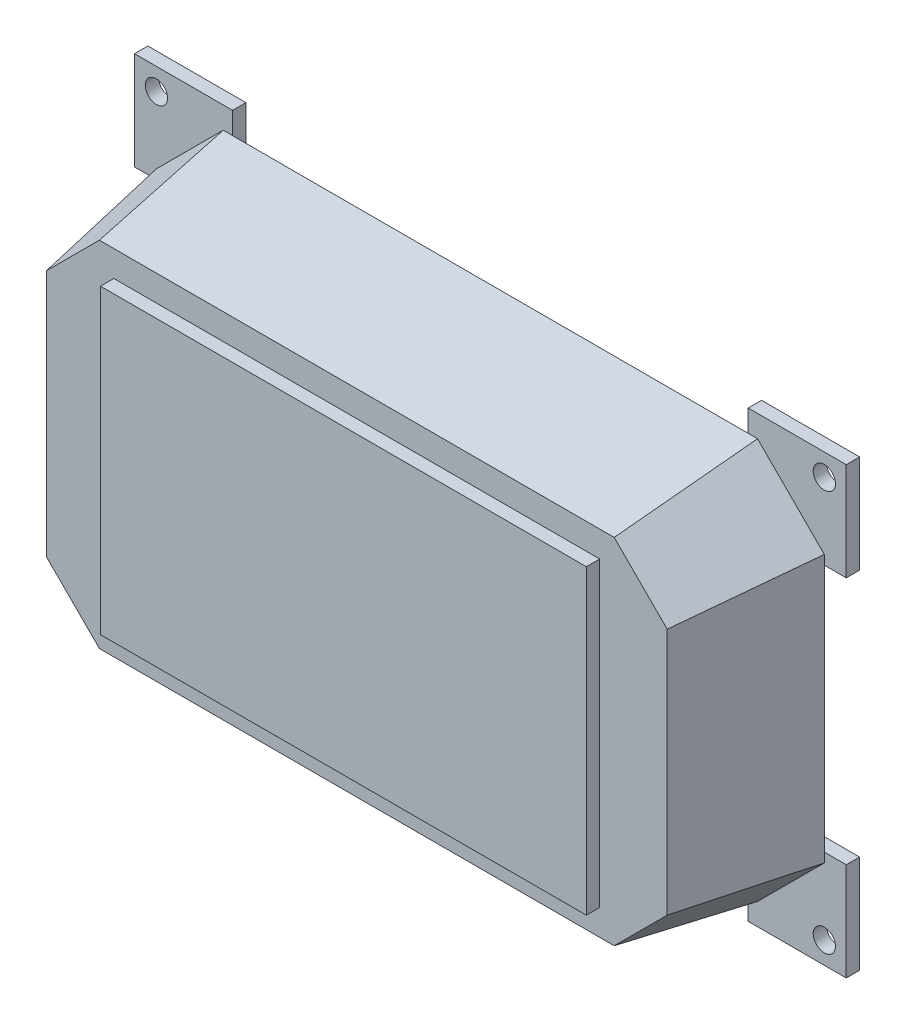
SolidWorks part; units mm, degrees
ref_plane "Front Plane" through (0, 0, 0) normal (0, 0, 1) x (1, 0, 0)
ref_plane "Top Plane" through (0, 0, 0) normal (0, 1, 0) x (1, 0, 0)
ref_plane "Right Plane" through (0, 0, 0) normal (1, 0, 0) x (0, 0, -1)
sketch "Sketch1" plane through (0, 0, 0) normal (0, 0, 1) x (1, 0, 0)
  line L0 (-100, 10.5319) -> (-85, 25.5319)
  line L1 (-85, 25.5319) -> (35, 25.5319)
  line L2 (-100, 10.5319) -> (-100, -49.4681)
  line L3 (-85, -64.4681) -> (35, -64.4681)
  line L4 (50, 10.5319) -> (50, -49.4681)
  line L5 (35, 25.5319) -> (50, 10.5319)
  line L6 (-100, -49.4681) -> (-85, -64.4681)
  line L7 (35, -64.4681) -> (50, -49.4681)
  point P0 (0, 0)
  point P1 (50, -64.4681)
  point P2 (-100, 25.5319)
  point P3 (-100, -64.4681)
  point P4 (50, 25.5319)
  dimension "D1" = 150
  dimension "D2" = 90
extrude "Boss-Extrude1" add sketch "Sketch1" along normal blind 30 draft 10
shell "Shell1" thickness 5
sketch "Sketch4" plane through (0, 0, -7) normal (0, 0, -1) x (-1, 0, 0)
  circle A0 centre (-24.7585, -65.1412) radius 1.5
  dimension "D1" = 3
extrude "Cut-Extrude1" cut sketch "Sketch4" against normal blind 15
ref_plane "Plane1" through (-26.0296, 0, 0) normal (1, 0, 0) x (0, 0, -1)
ref_plane "Plane2" through (0, -17.8507, 0) normal (0, 1, 0) x (1, 0, 0)
mirror "Mirror1" about plane through (-26.0296, 0, 0) normal (1, 0, 0) of "Cut-Extrude1"
sketch "Sketch5" plane through (0, 0, 30) normal (0, 0, 1) x (1, 0, 0)
  line L0 (32.8089, 20.2421) -> (-82.8089, 20.2421) construction
  line L1 (-79.5575, 14.4198) -> (29.5575, 14.4198)
  line L2 (-79.5575, 14.4198) -> (-79.5575, -53.356)
  line L3 (-79.5575, -53.356) -> (29.5575, -53.356)
  line L4 (29.5575, 14.4198) -> (29.5575, -53.356)
  line L5 (-79.5575, 14.4198) -> (29.5575, -53.356) construction
  line L6 (-79.5575, -53.356) -> (29.5575, 14.4198) construction
  line L7 (44.7102, -47.277) -> (44.7102, 8.3408) construction
  point P0 (-25, -19.4681)
  point P8 (-25, 20.2421)
  point P11 (44.7102, -19.4681)
  point P12 (29.5575, -19.4681)
extrude "Boss-Extrude3" add sketch "Sketch5" along normal blind 3
ref_plane "Plane3" through (0, -19.4681, 0) normal (0, 1, 0) x (1, 0, 0)
ref_plane "Plane4" through (-25, 0, 0) normal (1, 0, 0) x (0, 0, -1)
ref_plane "Plane5" through (0, -19.4681, 0) normal (0, 1, 0) x (1, 0, 0)
ref_plane "Plane6" through (-25, 0, 0) normal (-1, 0, 0) x (0, 0, 1)
sketch "Sketch8" plane through (0, 0, 0) normal (0, 0, -1) x (-1, 0, 0)
  line L5 (-54.9229, 8.4289) -> (-44.9229, 8.4289)
  line L6 (-54.9229, 30.4548) -> (-54.9229, 8.4289)
  line L7 (-32.897, 30.4548) -> (-54.9229, 30.4548)
  line L8 (-32.897, 20.4548) -> (-32.897, 30.4548)
  line L9 (-44.9229, 8.4289) -> (-32.897, 20.4548)
  line L10 (-54.9229, 8.4289) -> (-44.9229, 8.4289)
  line L11 (-54.9229, 30.4548) -> (-54.9229, 8.4289)
  line L12 (-32.897, 30.4548) -> (-54.9229, 30.4548)
  line L13 (-32.897, 20.4548) -> (-32.897, 30.4548)
  line L14 (-44.9229, 8.4289) -> (-32.897, 20.4548)
  dimension "D1" = 0
extrude "Boss-Extrude5" add sketch "Sketch8" along normal blind 3
mirror "Mirror4" about plane through (-25, 0, 0) normal (-1, 0, 0) of "Boss-Extrude5"
mirror "Mirror5" about plane through (0, -19.4681, 0) normal (0, 1, 0) of "Boss-Extrude5", "Mirror4"
sketch "Sketch9" plane through (0, 0, 0) normal (0, 0, 1) x (1, 0, 0)
  circle A0 centre (50, -64.4681) radius 2.5 construction
  circle A1 centre (50, -64.4681) radius 2.5
extrude "Cut-Extrude2" cut sketch "Sketch9" against normal through all both and the other way through all
mirror "Mirror6" about plane through (-25, 0, 0) normal (-1, 0, 0) of "Cut-Extrude2"
mirror "Mirror7" about plane through (0, -19.4681, 0) normal (0, 1, 0) of "Cut-Extrude2", "Mirror6"
